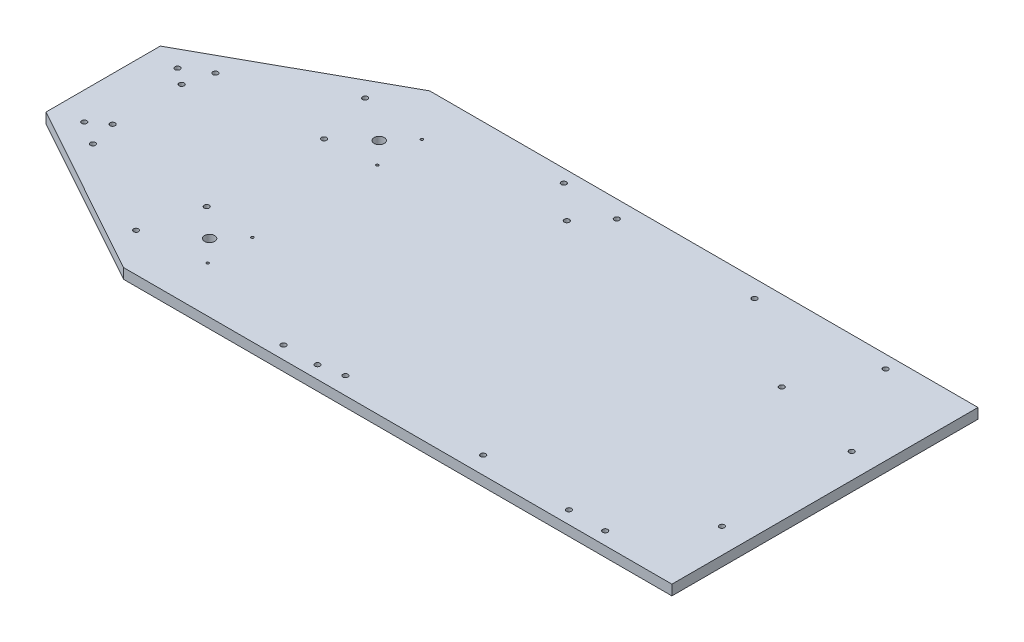
SolidWorks part; units mm, degrees
ref_plane "Front Plane" through (0, 0, 0) normal (0, 0, 1) x (1, 0, 0)
ref_plane "Top Plane" through (0, 0, 0) normal (0, 1, 0) x (1, 0, 0)
ref_plane "Right Plane" through (0, 0, 0) normal (1, 0, 0) x (0, 0, -1)
sketch "Sketch2" plane through (0, 0, 0) normal (0, 1, 0) x (1, 0, 0)
  line L0 (-264.5434, 98.7245) -> (-264.5434, 27.6045)
  line L1 (-156.5934, 158.4145) -> (184.7191, 158.4145)
  line L3 (-156.5934, -32.0855) -> (184.7191, -32.0855)
  line L4 (184.7191, 158.4145) -> (184.7191, -32.0855)
  line L10 (-264.5434, 27.6045) -> (-156.5934, -32.0855)
  line L11 (-264.5434, 98.7245) -> (-156.5934, 158.4145)
  dimension "D3" = 107.95
  dimension "D5" = 71.12
extrude "Boss-Extrude1" add sketch "Sketch2" along normal blind 6.35 contours L0 L10 L3 L4 L1 L11
sketch "Sketch4" plane through (0, 6.35, 0) normal (0, 1, 0) x (1, 0, 0)
  circle A0 centre (135.1891, 150.4135) radius 1.5875
  circle A1 centre (169.0981, 14.6505) radius 1.5875
  circle A2 centre (169.0981, 95.4225) radius 1.5875
  circle A3 centre (112.5831, 108.3765) radius 1.5875
  circle A4 centre (56.4491, 147.6195) radius 1.5875
  circle A5 centre (-29.2759, 147.6195) radius 1.5875
  circle A6 centre (-65.0645, 150.4135) radius 1.5875
  circle A7 centre (-43.8809, 131.1095) radius 1.5875
  circle A8 centre (-132.7809, 129.8395) radius 0.795
  circle A9 centre (-132.7809, 102.0583) radius 0.795
  circle A10 centre (-145.5018, 115.9489) radius 3.175
  circle A11 centre (-237.2384, 84.7545) radius 1.5875
  circle A12 centre (-237.2384, 41.7597) radius 1.5875
  circle A13 centre (-163.5784, 26.652) radius 1.5875
  circle A14 centre (-163.5784, 99.677) radius 1.5875
  circle A15 centre (-247.2714, 34.1397) radius 1.5875
  circle A16 centre (-247.2714, 92.1894) radius 1.5875
  circle A17 centre (-232.7934, 25.0645) radius 1.5875
  circle A18 centre (-172.7772, -8.1209) radius 1.5875
  circle A19 centre (-172.7772, 134.45) radius 1.5875
  circle A20 centre (-232.7934, 101.2645) radius 1.5875
  circle A21 centre (-132.7809, -3.5105) radius 0.795
  circle A22 centre (-132.7809, 24.2708) radius 0.795
  circle A23 centre (-145.5018, 10.3802) radius 3.175
  circle A25 centre (-43.8809, -24.0845) radius 1.5875
  circle A26 centre (-29.2759, -21.2905) radius 1.5875
  circle A27 centre (56.4491, -21.2905) radius 1.5875
  circle A28 centre (135.1891, -24.0845) radius 1.5875
  circle A29 centre (112.5831, -24.0845) radius 1.5875
  circle A30 centre (-65.0645, -24.0845) radius 1.5875
  point P0 (0, 0)
extrude "Cut-Extrude1" cut sketch "Sketch4" against normal through all
